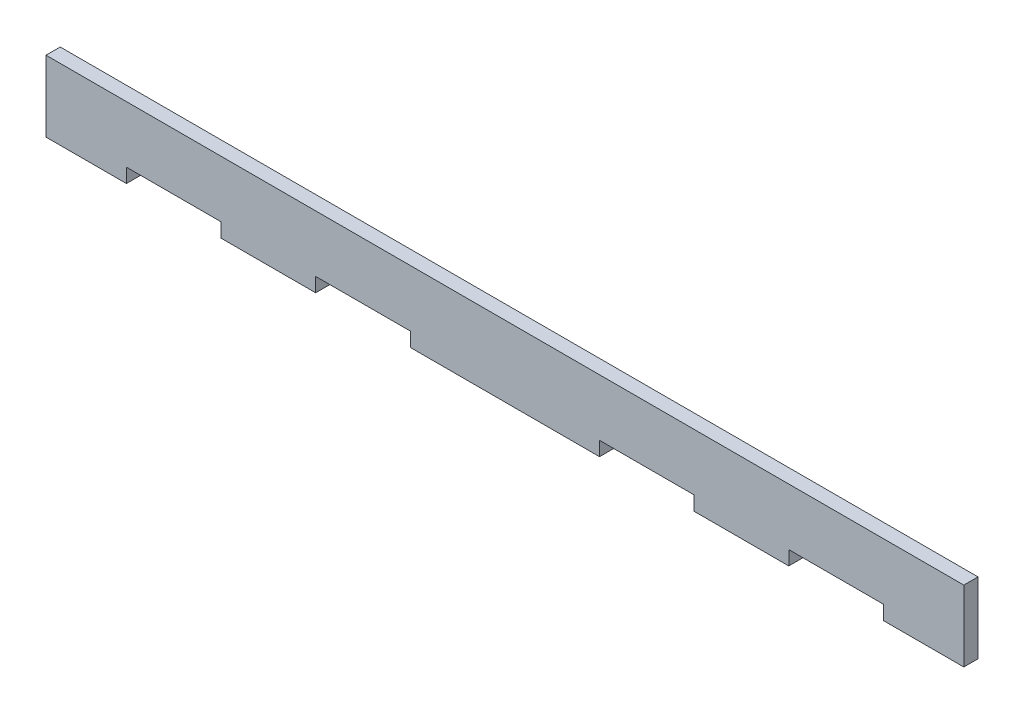
SolidWorks part; units mm, degrees
ref_plane "Front Plane" through (0, 0, 0) normal (0, 0, 1) x (1, 0, 0)
ref_plane "Top Plane" through (0, 0, 0) normal (0, 1, 0) x (1, 0, 0)
ref_plane "Right Plane" through (0, 0, 0) normal (1, 0, 0) x (0, 0, -1)
sketch "Sketch1" plane through (0, 0, 0) normal (0, 0, 1) x (1, 0, 0)
  line L1 (100, -7.5) -> (-100, -7.5)
  line L2 (100, -7.5) -> (100, 7.5)
  line L3 (100, 7.5) -> (-100, 7.5)
  line L4 (-100, -7.5) -> (-100, 7.5)
  line L5 (100, -7.5) -> (-100, 7.5) construction
  line L6 (100, 7.5) -> (-100, -7.5) construction
  point P0 (0, 0)
extrude "Boss-Extrude1" add sketch "Sketch1" along normal blind 3
sketch "Sketch2" plane through (0, 0, 3) normal (0, 0, 1) x (1, 0, 0)
  line L0 (-80, -4.5) -> (-60, -4.5)
  line L1 (97, -7.5) -> (100, -7.5)
  line L2 (-97, 7.5) -> (-97, -7.5)
  line L3 (-80, -7.5) -> (-60, -7.5)
  line L4 (-100, 7.5) -> (-100, -7.5)
  line L5 (-100, -7.5) -> (100, -7.5)
  line L6 (100, -7.5) -> (100, 7.5)
  line L7 (100, 7.5) -> (-100, 7.5)
  line L8 (-100, 7.5) -> (-100, -7.5)
  line L9 (-100, -7.5) -> (-97, -7.5)
  line L10 (100, -7.5) -> (100, 7.5)
  line L11 (100, 7.5) -> (97, 7.5)
  line L12 (-40, -4.5) -> (-20, -4.5)
  line L13 (20, -4.5) -> (40, -4.5)
  line L14 (60, -4.5) -> (80, -4.5)
  line L15 (97, -7.5) -> (97, 7.5)
  line L21 (-97, 7.5) -> (-100, 7.5)
  line L29 (-80, -4.5) -> (-80, -7.5)
  line L30 (-60, -4.5) -> (-60, -7.5)
  line L31 (-40, -4.5) -> (-40, -7.5)
  line L32 (-20, -4.5) -> (-20, -7.5)
  line L34 (20, -4.5) -> (20, -7.5)
  line L35 (40, -4.5) -> (40, -7.5)
  line L36 (60, -4.5) -> (60, -7.5)
  line L37 (80, -4.5) -> (80, -7.5)
  line L39 (-40, -7.5) -> (-20, -7.5)
  line L41 (60, -7.5) -> (80, -7.5)
  line L43 (20, -7.5) -> (40, -7.5)
  dimension "D1" = 0
extrude "Cut-Extrude2" cut sketch "Sketch2" against normal blind 3
